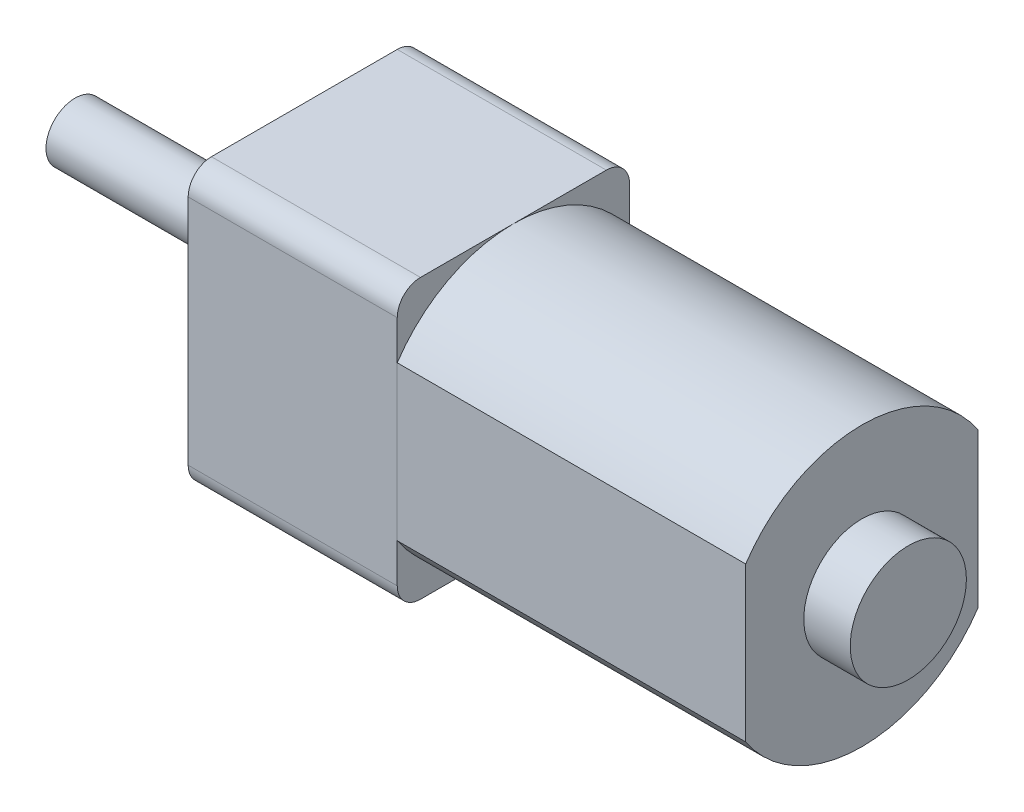
SolidWorks part; units mm, degrees
ref_plane "Front Plane" through (0, 0, 0) normal (0, 0, 1) x (1, 0, 0)
ref_plane "Top Plane" through (0, 0, 0) normal (0, 1, 0) x (1, 0, 0)
ref_plane "Right Plane" through (0, 0, 0) normal (1, 0, 0) x (0, 0, -1)
sketch "Sketch1" plane through (0, 0, 0) normal (1, 0, 0) x (0, 0, -1)
  line L0 (0, 6) -> (0, -6) construction
  line L1 (-5, 3.3166) -> (-5, -3.3166)
  line L2 (5, 3.3166) -> (5, -3.3166)
  arc A0 (-5, -3.3166) -> (5, -3.3166) centre (0, 0) ccw
  arc A1 (5, 3.3166) -> (-5, 3.3166) centre (0, 0) ccw
  dimension "D2" = 12
  dimension "D1" = 5
extrude "Extrude1" add sketch "Sketch1" against normal blind 15
sketch "Sketch2" plane through (-15, 0, 0) normal (-1, 0, 0) x (0, 0, 1)
  line L1 (-5, -6) -> (5, -6)
  line L2 (-5, -6) -> (-5, 6)
  line L3 (-5, 6) -> (5, 6)
  line L4 (5, -6) -> (5, 6)
  line L5 (-5, -6) -> (5, 6) construction
  line L6 (-5, 6) -> (5, -6) construction
  circle A0 centre (0, 0) radius 1.4045
  dimension "D1" = 10
  dimension "D2" = 12
extrude "Extrude2" add sketch "Sketch2" along normal blind 9 separate body
sketch "Sketch3" plane through (0, 0, 0) normal (1, 0, 0) x (0, 0, -1)
  circle A0 centre (0, 0) radius 2.5
  dimension "D1" = 5
extrude "Extrude3" add sketch "Sketch3" along normal blind 2 separate body
sketch "Sketch4" plane through (-24, 0, 0) normal (-1, 0, 0) x (0, 0, 1)
  circle A0 centre (0, 0) radius 1.95
  dimension "D1" = 3.9
extrude "Extrude4" add sketch "Sketch4" along normal blind 0.6 separate body
sketch "Sketch5" plane through (-24.6, 0, 0) normal (-1, 0, 0) x (0, 0, 1)
  circle A0 centre (0, 0) radius 1.25
  dimension "D1" = 2.5
extrude "Extrude5" add sketch "Sketch5" along normal blind 9.27
fillet "Fillet1" radius 1 4 edges at (-19.5, -6, -5) (-19.5, -6, 5) (-19.5, 6, -5) (-19.5, 6, 5)
